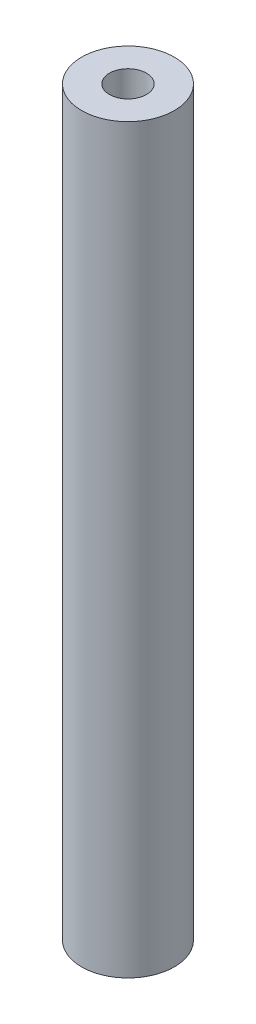
SolidWorks part; units mm, degrees
ref_plane "Front" through (0, 0, 0) normal (0, 0, 1) x (1, 0, 0)
ref_plane "Top" through (0, 0, 0) normal (0, 1, 0) x (1, 0, 0)
ref_plane "Right" through (0, 0, 0) normal (1, 0, 0) x (0, 0, -1)
sketch "Sketch1" plane through (0, 0, 0) normal (0, 1, 0) x (1, 0, 0)
  circle A0 centre (0, 0) radius 2.5
  circle A1 centre (0, 0) radius 1
  dimension "D1" = 2
  dimension "D2" = 1.5
extrude "Boss-Extrude1" add sketch "Sketch1" along normal blind 40
